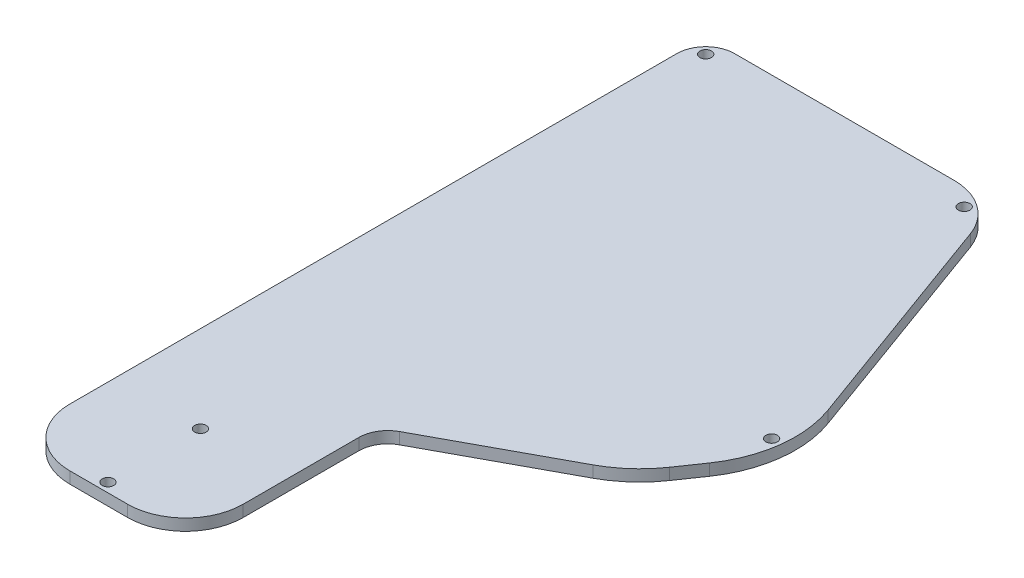
SolidWorks part; units mm, degrees
ref_plane "Front Plane" through (0, 0, 0) normal (0, 0, 1) x (1, 0, 0)
ref_plane "Top Plane" through (0, 0, 0) normal (0, 1, 0) x (1, 0, 0)
ref_plane "Right Plane" through (0, 0, 0) normal (1, 0, 0) x (0, 0, -1)
sketch "Sketch2" plane through (0, 0, 0) normal (0, 1, 0) x (1, 0, 0)
  line L0 (12.7, 0) -> (25.4, 0)
  line L1 (38.1, 12.7) -> (38.1, 38.1)
  line L2 (0, 12.7) -> (0, 146.05)
  line L3 (6.35, 152.4) -> (54.584, 152.4)
  line L7 (30.467, 152.4) -> (30.467, 82.55) construction
  line L8 (66.5181, 144.0437) -> (84.4217, 94.854)
  line L9 (0, 82.55) -> (88.9, 82.55) construction
  line L10 (81.4758, 71.7646) -> (77.8753, 66.5341)
  line L11 (69.0225, 58.5869) -> (41.4326, 43.6873)
  arc A0 (25.4, 0) -> (38.1, 12.7) centre (25.4, 12.7) ccw
  arc A1 (12.7, 0) -> (0, 12.7) centre (12.7, 12.7) cw
  arc A2 (0, 146.05) -> (6.35, 152.4) centre (6.35, 146.05) cw
  arc A8 (54.584, 152.4) -> (66.5181, 144.0437) centre (54.584, 139.7) cw
  arc A9 (84.4217, 94.854) -> (81.4758, 71.7646) centre (60.5535, 86.1667) cw
  arc A10 (77.8753, 66.5341) -> (69.0225, 58.5869) centre (56.953, 80.9361) cw
  arc A11 (41.4326, 43.6873) -> (38.1, 38.1) centre (44.45, 38.1) ccw
  point P8 (38.1, 41.8876)
  point P10 (38.1, 0)
  point P13 (0, 0)
  point P16 (0, 152.4)
  point P22 (63.4767, 152.4)
  point P29 (74.406, 61.4942)
  point P33 (38.1, 41.8876)
  dimension "D4" = 12.7
  dimension "D6" = 6.35
  dimension "D9" = 12.7
  dimension "D11" = 6.35
  dimension "D12" = 25.4
  dimension "D10" = 25.4
  dimension "D13" = 6.35
  dimension "D1" = 152.4
  dimension "D2" = 110
  dimension "D3" = 38.1
  dimension "D5" = 25.4
  dimension "D7" = 69.85
  dimension "D8" = 88.9
extrude "OHGC BASE" add sketch "Sketch2" along normal blind 2.54
sketch "Sketch7" plane through (0, 0, 0) normal (0, 1, 0) x (1, 0, 0)
  line L0 (54.584, 152.4) -> (6.35, 152.4) construction
  line L2 (0, 146.05) -> (0, 12.7) construction
  line L3 (84.4217, 94.854) -> (66.5181, 144.0437) construction
  line L4 (77.8753, 66.5341) -> (81.4758, 71.7646) construction
  line L5 (12.7, 0) -> (25.4, 0) construction
  line L6 (19.05, 0) -> (19.05, 2.032) construction
  circle A0 centre (3.302, 149.098) radius 1.27
  circle A1 centre (60.72, 148.463) radius 1.27
  circle A2 centre (83.6559, 83.2191) radius 1.27
  circle A3 centre (19.05, 22.352) radius 1.27
  circle A4 centre (19.05, 2.032) radius 1.27
  dimension "D1" = 2.54
  dimension "D2" = 3.302
  dimension "D3" = 3.302
  dimension "D4" = 3.937
  dimension "D5" = 3.937
  dimension "D6" = 4.699
  dimension "D7" = 4.699
  dimension "D8" = 2.032
  dimension "D9" = 20.32
extrude "Screwholes" cut sketch "Sketch7" along normal through all
